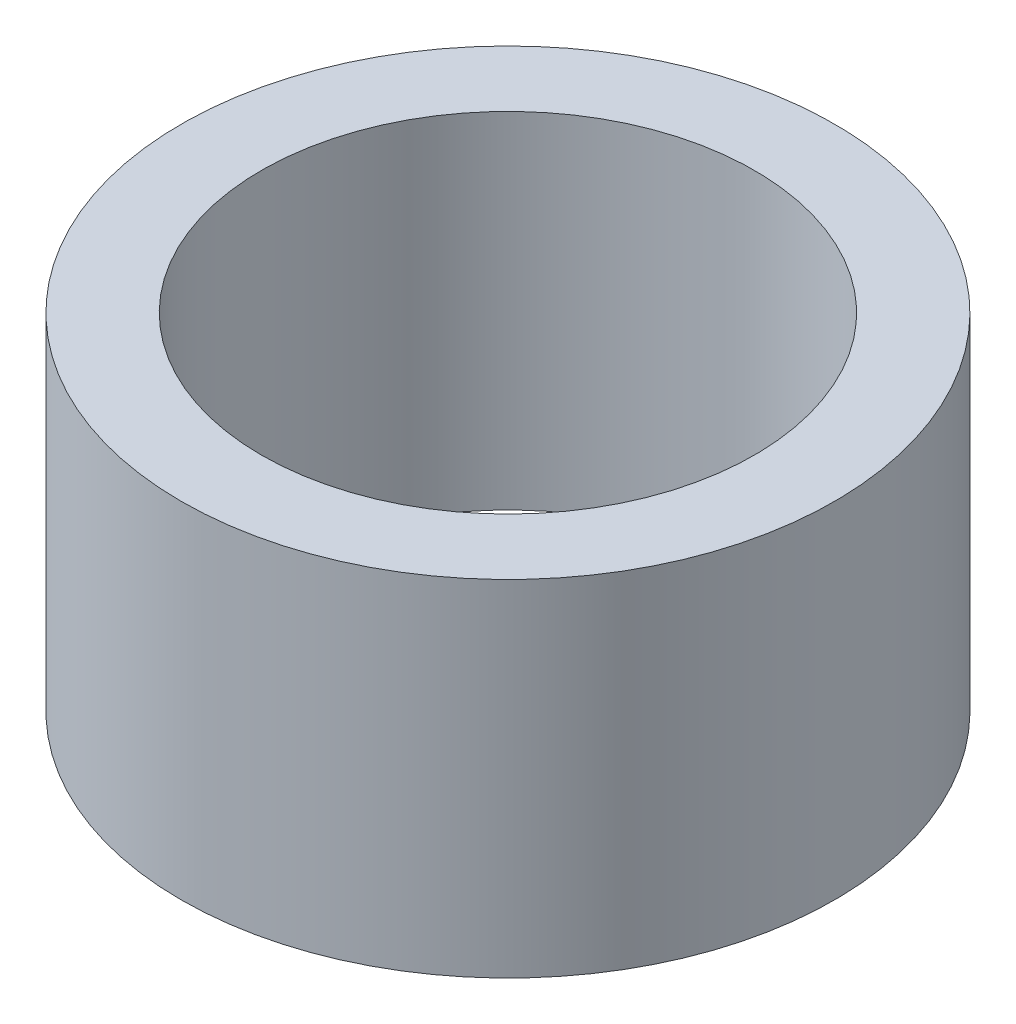
SolidWorks part; units mm, degrees
ref_plane "Front Plane" through (0, 0, 0) normal (0, 0, 1) x (1, 0, 0)
ref_plane "Top Plane" through (0, 0, 0) normal (0, 1, 0) x (1, 0, 0)
ref_plane "Right Plane" through (0, 0, 0) normal (1, 0, 0) x (0, 0, -1)
sketch "Sketch1" plane through (0, 0, 0) normal (0, 1, 0) x (1, 0, 0)
  circle A0 centre (0, 0) radius 13.25
  circle A1 centre (0, 0) radius 10
  dimension "D1" = 26.5
  dimension "D2" = 20
extrude "Boss-Extrude1" add sketch "Sketch1" along normal blind 14
